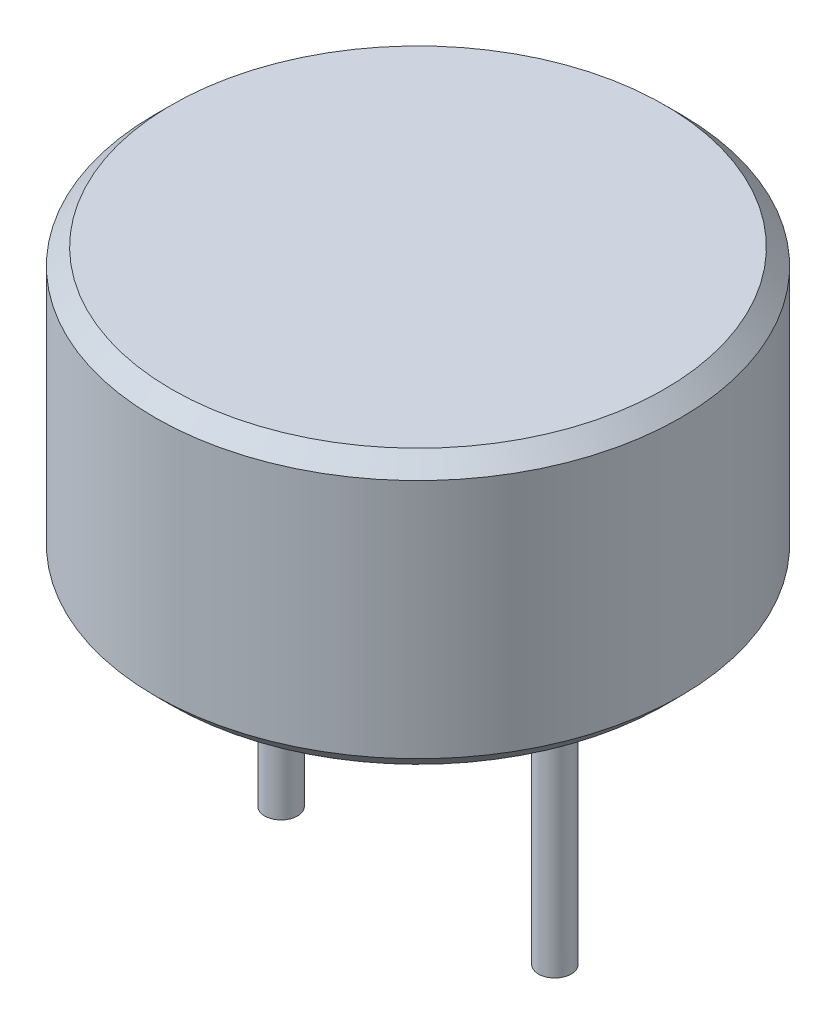
SolidWorks part; units mm, degrees
ref_plane "前视基准面" through (0, 0, 0) normal (0, 0, 1) x (1, 0, 0)
ref_plane "上视基准面" through (0, 0, 0) normal (0, 1, 0) x (1, 0, 0)
ref_plane "右视基准面" through (0, 0, 0) normal (1, 0, 0) x (0, 0, -1)
sketch "草图1" plane through (0, 0, 0) normal (0, 1, 0) x (1, 0, 0)
  circle A0 centre (0, 0) radius 4.8
  dimension "D1" = 9.6
extrude "凸台-拉伸1" add sketch "草图1" along normal blind 5
chamfer "倒角1" distance 0.3 angle 45 2 edges at (0, 0, 4.8) (0, 5, 4.8)
sketch "草图2" plane through (0, 0, 0) normal (0, -1, 0) x (1, 0, 0)
  line L0 (-2.5, 0) -> (2.5, 0)
  circle A0 centre (-2.5, 0) radius 0.3
  circle A1 centre (2.5, 0) radius 0.3
  point P4 (0, 0)
  dimension "D2" = 0.6
  dimension "D3" = 0.6
  dimension "D1" = 5
extrude "凸台-拉伸2" add sketch "草图2" along normal blind 5.1 contours A0 | A1
